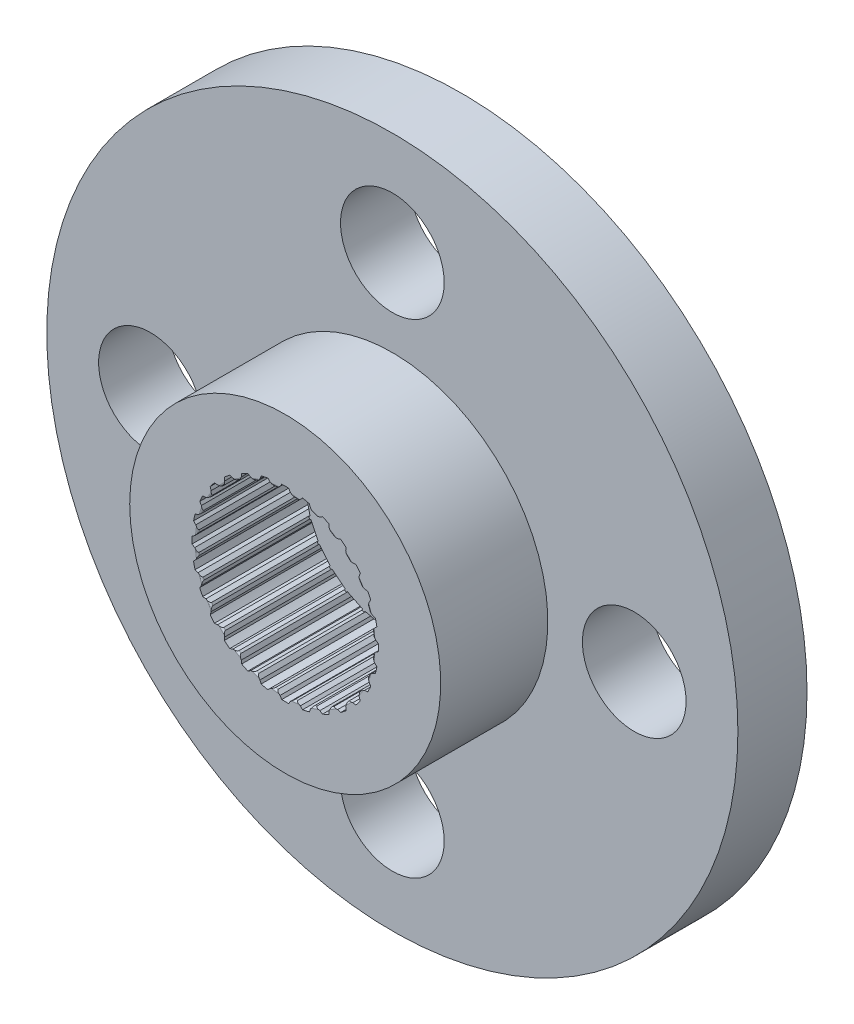
SolidWorks part; units mm, degrees
material "Beryllium"
ref_plane "Alzado" through (0, 0, 0) normal (0, 0, 1) x (1, 0, 0)
ref_plane "Planta" through (0, 0, 0) normal (0, 1, 0) x (1, 0, 0)
ref_plane "Vista lateral" through (0, 0, 0) normal (1, 0, 0) x (0, 0, -1)
sketch "Croquis1" plane through (0, 0, 0) normal (0, 0, 1) x (1, 0, 0)
  circle A0 centre (0, 0) radius 7 construction
  circle A1 centre (0, 0) radius 10
  circle A2 centre (-7, 0) radius 1.5
  circle A3 centre (0, 7) radius 1.5
  circle A4 centre (0, -7) radius 1.5
  circle A5 centre (7, 0) radius 1.5
  circle A6 centre (0, 0) radius 1.5
  dimension "D1" = 14
  dimension "D2" = 20
  dimension "D3" = 3
extrude "Saliente-Extruir1" add sketch "Croquis1" along normal blind 2
sketch "Croquis3" plane through (0, 0, 2) normal (0, 0, 1) x (1, 0, 0)
  line L0 (0, 0) -> (0, 4.1004) construction
  circle A0 centre (0, 0) radius 4.5
  circle A1 centre (0, 0) radius 2.55
  point P4 (0, 4.1004)
  dimension "D1" = 9
  dimension "D2" = 5.1
extrude "Saliente-Extruir3" add sketch "Croquis3" along normal blind 3.1
sketch "Croquis4" plane through (0, 0, 5.1) normal (0, 0, 1) x (1, 0, 0)
  line L0 (0, 0) -> (0, 3.2695) construction
  line L1 (0.246, 2.4975) -> (-0.246, 2.4975)
  line L2 (-0.246, 2.4975) -> (-0.25, 2.5377)
  line L3 (-0.25, 2.5377) -> (-0.15, 2.62)
  line L4 (-0.15, 2.62) -> (-0.1, 2.6981)
  line L5 (0.246, 2.4975) -> (0.25, 2.5377)
  line L6 (0.25, 2.5377) -> (0.15, 2.62)
  line L7 (0.15, 2.62) -> (0.1, 2.6981)
  circle A0 centre (0, 0) radius 2.55
  circle A1 centre (0, 0) radius 2.7
  point P7 (-0.1689, 2.6947)
  point P11 (-0.1266, 2.6144)
  point P12 (0, 0)
  point P13 (0, 2.4975)
  point P15 (0, 2.4975)
  point P18 (0, 0)
  circle M7 centre (0, 0) radius 2.55
  dimension "D1" = 5.1
  dimension "D2" = 5.4
  dimension "D7" = 2.4975
  dimension "D3" = 0.25
  dimension "D4" = 0.15
  dimension "D5" = 0.1
  dimension "D6" = 2.62
extrude "Cortar-Extruir2" cut sketch "Croquis4" against normal blind 3.4 contours L0 A0 L6 L7 A1 | L0 A1 L4 L3 M7 | L0 L1 L5 A0 | L1 L0 L2 M7
fillet "Redondeo1" radius 0.05 1 edges at (0, -2.55, 5.1)
pattern_circular "MatrizC1" count 28 over 360 about axis through (0, 0, 0) along (0, 0, 1) of "Cortar-Extruir2"
